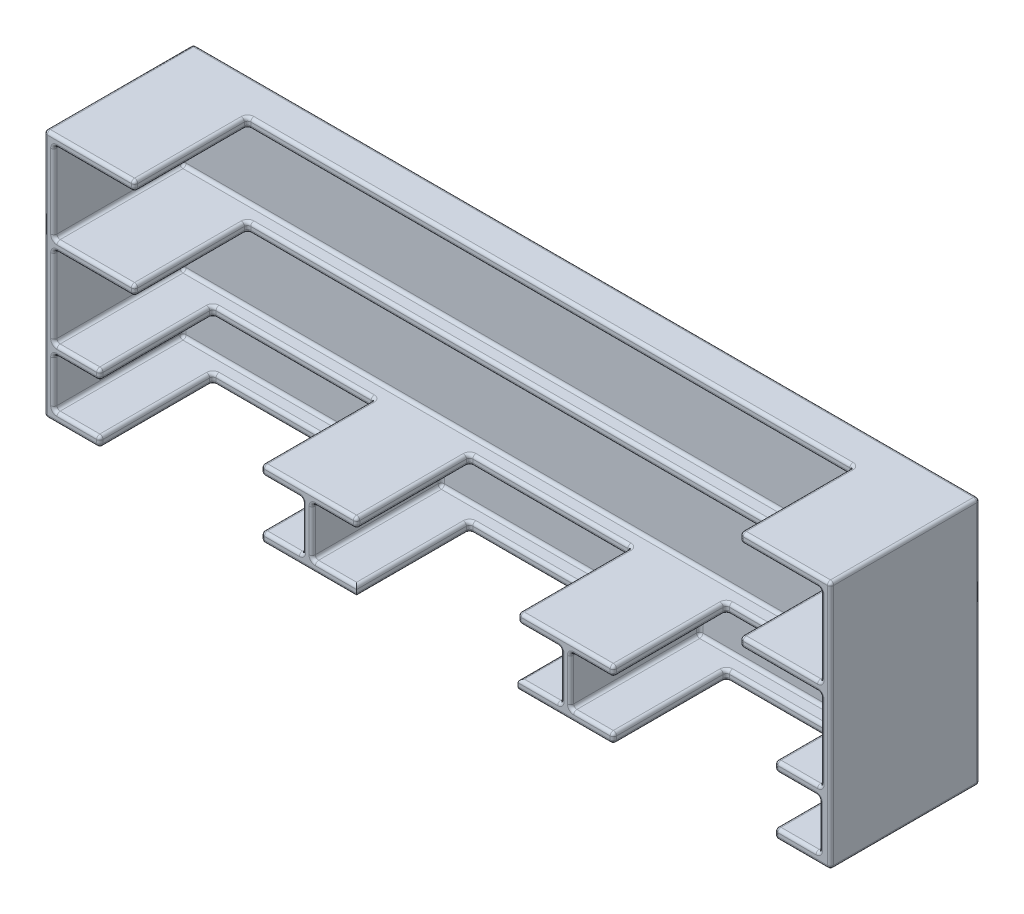
SolidWorks part; units mm, degrees
ref_plane "Front Plane" through (0, 0, 0) normal (0, 0, 1) x (1, 0, 0)
ref_plane "Top Plane" through (0, 0, 0) normal (0, 1, 0) x (1, 0, 0)
ref_plane "Right Plane" through (0, 0, 0) normal (1, 0, 0) x (0, 0, -1)
sketch "Sketch1" plane through (0, 0, 0) normal (0, 0, 1) x (1, 0, 0)
  line L1 (0, 0) -> (-123.698, 0)
  line L2 (0, 0) -> (0, 39.116)
  line L3 (0, 39.116) -> (-123.698, 39.116)
  line L4 (-123.698, 0) -> (-123.698, 39.116)
  line L5 (-122.174, 37.592) -> (-1.524, 37.592)
  line L6 (-122.174, 37.592) -> (-122.174, 24.892)
  line L7 (-122.174, 24.892) -> (-1.524, 24.892)
  line L8 (-1.524, 37.592) -> (-1.524, 24.892)
  line L9 (-122.174, 23.368) -> (-1.524, 23.368)
  line L10 (-122.174, 23.368) -> (-122.174, 10.668)
  line L11 (-122.174, 10.668) -> (-1.524, 10.668)
  line L12 (-1.524, 23.368) -> (-1.524, 10.668)
  line L13 (-122.174, 9.144) -> (-83.058, 9.144)
  line L14 (-122.174, 9.144) -> (-122.174, 1.524)
  line L15 (-122.174, 1.524) -> (-83.058, 1.524)
  line L16 (-83.058, 9.144) -> (-83.058, 1.524)
  line L17 (-81.534, 9.144) -> (-42.418, 9.144)
  line L18 (-81.534, 9.144) -> (-81.534, 1.524)
  line L19 (-81.534, 1.524) -> (-42.418, 1.524)
  line L20 (-42.418, 9.144) -> (-42.418, 1.524)
  line L21 (-40.894, 9.144) -> (-1.778, 9.144)
  line L22 (-40.894, 9.144) -> (-40.894, 1.524)
  line L23 (-40.894, 1.524) -> (-1.778, 1.524)
  line L24 (-1.778, 9.144) -> (-1.778, 1.524)
  point P25 (-122.174, 5.334)
  point P26 (-81.534, 5.334)
  dimension "D1" = 120.65
  dimension "D2" = 1.524
  dimension "D3" = 1.524
  dimension "D4" = 12.7
  dimension "D5" = 12.7
  dimension "D6" = 1.524
  dimension "D7" = 1.524
  dimension "D8" = 1.524
  dimension "D9" = 7.62
  dimension "D10" = 39.116
  dimension "D11" = 39.116
  dimension "D12" = 39.116
  dimension "D13" = 1.524
  dimension "D14" = 1.524
  dimension "D16" = 1.524
  dimension "D15" = 1.524
extrude "Boss-Extrude1" add sketch "Sketch1" along normal blind 20.32
sketch "Sketch3" plane through (0, 0, 20.32) normal (0, 0, 1) x (1, 0, 0)
  line L0 (0, 39.116) -> (-123.698, 39.116) construction
  line L1 (-14.224, 39.116) -> (-109.474, 39.116)
  line L2 (-14.224, 39.116) -> (-14.224, 10.668)
  line L3 (-14.224, 10.668) -> (-109.474, 10.668)
  line L4 (-109.474, 39.116) -> (-109.474, 10.668)
  line L5 (-122.174, 10.668) -> (-1.524, 10.668) construction
  line L7 (-1.524, 10.668) -> (-1.524, 23.368) construction
  line L9 (-122.174, 23.368) -> (-122.174, 10.668) construction
  dimension "D1" = 12.7
  dimension "D2" = 12.7
extrude "Cut-Extrude1" cut sketch "Sketch3" against normal blind 17.78
sketch "Sketch4" plane through (0, 0, 0) normal (0, -1, 0) x (-1, 0, 0)
  line L1 (114.935, -2.54) -> (89.535, -2.54)
  line L2 (114.935, -2.54) -> (114.935, -40.64)
  line L3 (114.935, -40.64) -> (89.535, -40.64)
  line L4 (89.535, -2.54) -> (89.535, -40.64)
  line L5 (74.549, -2.54) -> (49.149, -2.54)
  line L6 (74.549, -2.54) -> (74.549, -40.64)
  line L7 (74.549, -40.64) -> (49.149, -40.64)
  line L8 (49.149, -2.54) -> (49.149, -40.64)
  line L9 (34.163, -2.54) -> (8.763, -2.54)
  line L10 (34.163, -2.54) -> (34.163, -40.64)
  line L11 (34.163, -40.64) -> (8.763, -40.64)
  line L12 (8.763, -2.54) -> (8.763, -40.64)
  line L15 (123.698, -20.32) -> (0, -20.32) construction
  point P12 (21.463, -40.64)
  point P13 (102.235, -40.64)
  point P18 (61.849, -20.32)
  point P21 (61.849, -40.64)
  dimension "D1" = 25.4
  dimension "D2" = 25.4
  dimension "D3" = 25.4
  dimension "D4" = 21.463
  dimension "D5" = 21.463
  dimension "D6" = 38.1
  dimension "D7" = 17.78
extrude "Cut-Extrude2" cut sketch "Sketch4" against normal up to surface (10.668 mm away) up to face at (-61.849, 10.668, 10.16)
sketch "Sketch2" plane through (0, 0, 0) normal (0, 0, -1) x (-1, 0, 0)
  line L1 (0, 0) -> (123.698, 0)
  line L2 (0, 0) -> (0, 39.116)
  line L3 (0, 39.116) -> (123.698, 39.116)
  line L4 (123.698, 0) -> (123.698, 39.116)
extrude "Boss-Extrude2" add sketch "Sketch2" along normal blind 3.175
fillet "Fillet1" radius 0.5 26 edges at (-21.463, 0, 2.54) (-89.535, 10.668, 11.43) (-34.163, 1.524, 11.43) (-21.463, 1.524, 2.54) (-8.763, 1.524, 11.43) (-74.549, 1.524, 11.43) (0, 19.558, -3.175) (-61.849, 39.116, -3.175) (-102.616, 1.524, 0) (-118.5545, 9.144, 20.32) (-86.2965, 9.144, 20.32) (-83.058, 9.144, 10.16) (-61.849, 10.668, 0) (-122.174, 31.242, 0) (-122.174, 31.242, 20.32) (-1.524, 31.242, 20.32) (-1.524, 24.892, 10.16) (-14.224, 23.368, 11.43) (-89.535, 9.144, 11.43) (-78.0415, 9.144, 20.32) (-45.7835, 1.524, 20.32) (-5.1435, 10.668, 20.32) (-34.163, 9.906, 2.54) (-49.149, 9.906, 20.32) (-82.042, 0, 20.32) (-82.042, 10.668, 20.32)
equation "\"D14@Sketch1\"=\"D15@Sketch1\""
equation "\"D13@Sketch1\"=\"D15@Sketch1\""
equation "\"D8@Sketch1\"=\"D16@Sketch1\""
equation "\"D2@Sketch1\"=\"D8@Sketch1\""
equation "\"D7@Sketch1\"=\"D16@Sketch1\""
equation "\"D6@Sketch1\"=\"D16@Sketch1\""
equation "\"D3@Sketch1\"=\"D16@Sketch1\""
equation "\"D11@Sketch1\"=\"D12@Sketch1\""
equation "\"D10@Sketch1\"=\"D12@Sketch1\""
